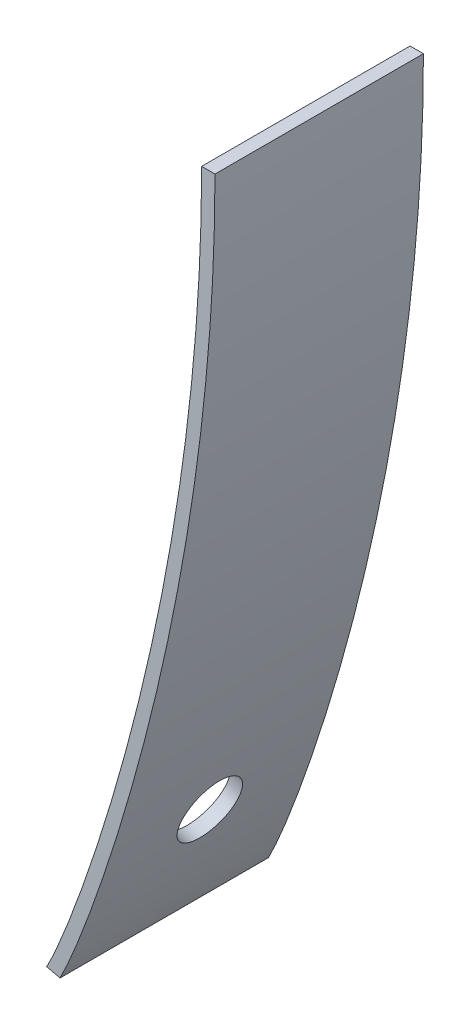
SolidWorks part; units mm, degrees
ref_plane "Front Plane" through (0, 0, 0) normal (0, 0, 1) x (1, 0, 0)
ref_plane "Top Plane" through (0, 0, 0) normal (0, 1, 0) x (1, 0, 0)
ref_plane "Right Plane" through (0, 0, 0) normal (1, 0, 0) x (0, 0, -1)
sketch "Sketch1" plane through (0, 0, 0) normal (0, 0, 1) x (1, 0, 0)
  line L0 (0, 29.3553) -> (0, 0) construction
  line L1 (0, 0) -> (-9.5996, -25.4183) construction
  line L2 (-9.5996, -25.4183) -> (-11.8001, -29.5747) construction
  line L3 (-1.016, 29.3553) -> (0, 29.3553)
  line L5 (-11.8001, -29.5747) -> (-12.8239, -29.337)
  line L6 (-12.8239, -29.337) -> (-12.6981, -29.0994)
  spline S0 degree 3 poles (0, 29.3553) (0, 0) (-9.5996, -25.4183) (-11.8001, -29.5747) knots 0 0 0 0 1 1 1 1
  spline S1 degree 1 poles (-1.016, 29.3553) (-12.6981, -29.0994) knots 0 0 1 1 construction
  spline S2 degree 3 poles (-1.016, 29.3553) (-1.016, 27.5503) (-1.0904, 23.9152) (-1.5043, 16.8554) (-2.457, 8.3615) (-4.0994, -1.0565) (-6.0427, -9.5056) (-7.7471, -15.5658) (-9.0619, -19.7231) (-9.9986, -22.4696) (-10.8605, -24.8184) (-11.4952, -26.4219) (-11.9393, -27.4773) (-12.2372, -28.1519) (-12.4511, -28.6092) (-12.6023, -28.9153) (-12.6643, -29.0356) (-12.6981, -29.0994) knots 0 0 0 0 0.0625 0.125 0.25 0.375 0.5 0.625 0.6875 0.75 0.8125 0.875 0.90625 0.9375 0.96875 0.984375 1 1 1 1
  dimension "D1" = 1.016
extrude "Boss-Extrude1" add sketch "Sketch1" along normal blind 15.875
sketch3d "3DSketch1"
  point P0 (-10.5897, -24.0711, 8.0106)
ref_plane "Plane1" through (-9.6372, -24.4248, 8.0106) normal (0.9374, -0.3481, 0) x (0, 0, -1)
ref_plane "Plane2" through (0, 0, 7.9375) normal (0, 0, 1) x (1, 0, 0)
ref_plane "Plane3" through (-5.3237, -22.9298, 0) normal (-0.2262, -0.9741, 0) x (-0.9741, 0.2262, 0)
sketch "Sketch4" plane through (-5.3237, -22.9298, 0) normal (-0.2262, -0.9741, 0) x (-0.9741, 0.2262, 0)
  point P0 (-2.3932, -7.9375)
sketch "Sketch3" plane through (-9.6372, -24.4248, 8.0106) normal (0.9374, -0.3481, 0) x (0, 0, -1)
  line L2 (-7.8644, -5.5808) -> (8.0106, -5.5808) construction
  line L3 (0.0731, 33.3051) -> (0.0731, 19.1988) construction
  circle A0 centre (0.0731, 3.9442) radius 2.3813
  point P0 (0.0731, 3.9442)
  dimension "D1" = 4.7625
  dimension "D2" = 9.525
extrude "Cut-Extrude1" cut sketch "Sketch3" against normal through all
ref_point "Point1" parameters "D1"=12.065
ref_point "Point2"
